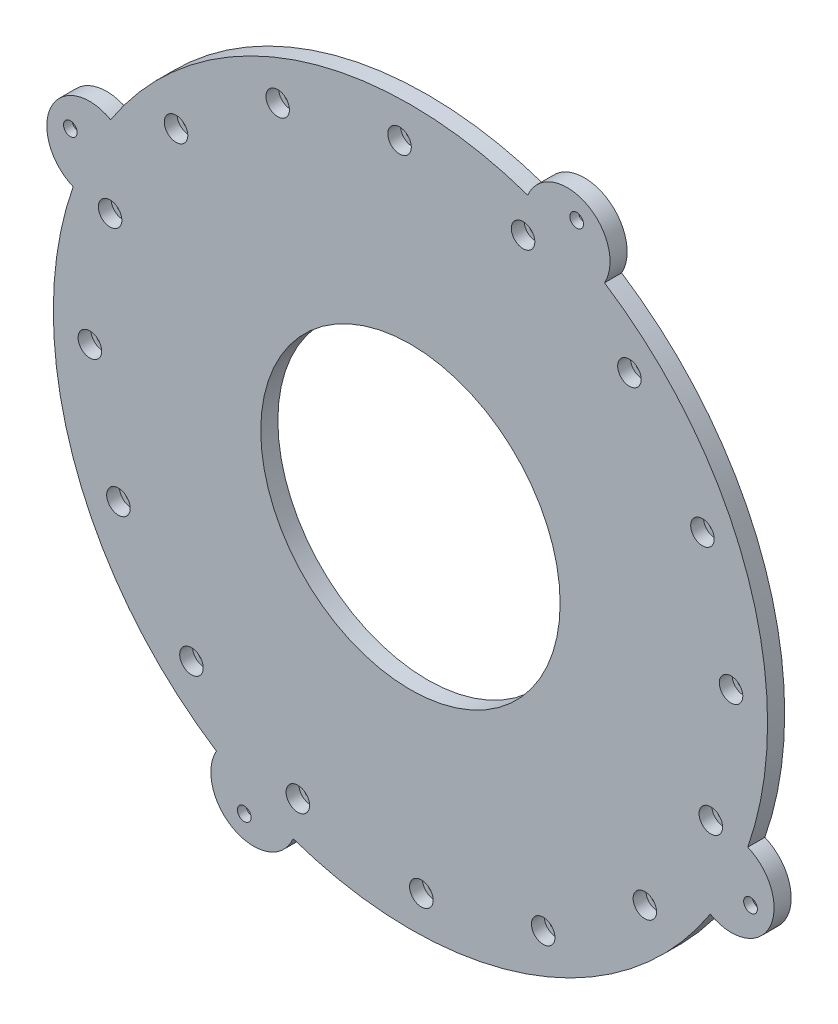
SolidWorks part; units mm, degrees
ref_plane "Front Plane" through (0, 0, 0) normal (0, 0, 1) x (1, 0, 0)
ref_plane "Top Plane" through (0, 0, 0) normal (0, 1, 0) x (1, 0, 0)
ref_plane "Right Plane" through (0, 0, 0) normal (1, 0, 0) x (0, 0, -1)
sketch "Sketch1" plane through (0, 0, 0) normal (0, 0, 1) x (1, 0, 0)
  circle A0 centre (-20.1422, -37.1244) radius 83.5
  circle A1 centre (-20.1422, -37.1244) radius 35
  circle A2 centre (-20.1422, -37.1244) radius 83.5 construction
  dimension "D1" = 70
extrude "Boss-Extrude1" add sketch "Sketch1" along normal blind 4
sketch "Sketch2" plane through (0, 0, 4) normal (0, 0, 1) x (1, 0, 0)
  circle A0 centre (-51.1825, 31.1507) radius 1.6
  circle A1 centre (-22.692, 37.8322) radius 1.6
  circle A2 centre (6.1868, 33.1023) radius 1.6
  circle A3 centre (31.0572, 17.6809) radius 1.6
  circle A4 centre (48.133, -6.084) radius 1.6
  circle A5 centre (54.8145, -34.5746) radius 1.6
  circle A6 centre (50.0845, -63.4534) radius 1.6
  circle A7 centre (34.6632, -88.3238) radius 1.6
  circle A8 centre (10.8982, -105.3996) radius 1.6
  circle A9 centre (-17.5924, -112.0811) radius 1.6
  circle A10 centre (-46.4711, -107.3511) radius 1.6
  circle A11 centre (-71.3415, -91.9297) radius 1.6
  circle A12 centre (-88.4173, -68.1648) radius 1.6
  circle A13 centre (-95.0988, -39.6742) radius 1.6
  circle A14 centre (-90.3688, -10.7954) radius 1.6
  circle A15 centre (-74.9475, 14.075) radius 1.6
  point P36 (-20.1422, -37.1244)
  dimension "D1" = 3.2
  dimension "D2" = 16
extrude "Cut-Extrude1" cut sketch "Sketch2" against normal up to next
sketch "Sketch3" plane through (0, 0, 4) normal (0, 0, 1) x (1, 0, 0)
  circle A0 centre (-74.9475, 14.075) radius 2.75
  circle A1 centre (-51.1825, 31.1507) radius 2.75
  circle A2 centre (-22.692, 37.8322) radius 2.75
  circle A3 centre (6.1868, 33.1023) radius 2.75
  circle A4 centre (31.0572, 17.6809) radius 2.75
  circle A5 centre (48.133, -6.084) radius 2.75
  circle A6 centre (54.8145, -34.5746) radius 2.75
  circle A7 centre (50.0845, -63.4534) radius 2.75
  circle A8 centre (34.6632, -88.3238) radius 2.75
  circle A9 centre (10.8982, -105.3996) radius 2.75
  circle A10 centre (-17.5924, -112.0811) radius 2.75
  circle A11 centre (-46.4711, -107.3511) radius 2.75
  circle A12 centre (-71.3415, -91.9297) radius 2.75
  circle A13 centre (-88.4173, -68.1648) radius 2.75
  circle A14 centre (-95.0988, -39.6742) radius 2.75
  circle A15 centre (-90.3688, -10.7954) radius 2.75
  point P35 (-20.1422, -37.1244)
  dimension "D1" = 5.5
  dimension "D2" = 16
extrude "Cut-Extrude2" cut sketch "Sketch3" against normal blind 3
sketch "Sketch4" plane through (0, 0, 4) normal (0, 0, 1) x (1, 0, 0)
  arc A0 (7.2931, 41.7398) -> (25.2294, 32.9732) centre (16.5242, 37.8944) cw
  circle A1 centre (-20.1422, -37.1244) radius 83.5 construction
  arc A2 (7.2931, 41.7398) -> (25.2294, 32.9732) centre (-20.1422, -37.1244) cw
  arc A3 (58.722, -64.5596) -> (49.9554, -82.496) centre (-20.1422, -37.1244) cw
  arc A4 (58.722, -64.5596) -> (49.9554, -82.496) centre (54.8767, -73.7908) cw
  arc A5 (-47.5774, -115.9886) -> (-65.5137, -107.222) centre (-20.1422, -37.1244) cw
  arc A6 (-47.5774, -115.9886) -> (-65.5137, -107.222) centre (-56.8085, -112.1433) cw
  arc A7 (-99.0063, -9.6892) -> (-90.2397, 8.2472) centre (-20.1422, -37.1244) cw
  arc A8 (-99.0063, -9.6892) -> (-90.2397, 8.2472) centre (-95.161, -0.4581) cw
  dimension "D1" = 10
  dimension "D2" = 4
extrude "Boss-Extrude2" add sketch "Sketch4" against normal up to surface (4 mm away) up to face at (-21.092, 37.8322, 0)
sketch "Sketch5" plane through (0, 0, 0) normal (0, 0, -1) x (-1, 0, 0)
  line L0 (61.1997, -121.1276) -> (56.8085, -112.1433) construction
  arc A0 (47.5774, -115.9886) -> (65.5137, -107.222) centre (56.8085, -112.1433) ccw construction
  circle A1 centre (59.0041, -116.6354) radius 1.6
  circle A2 centre (-59.3688, -75.9864) radius 1.6
  circle A3 centre (-18.7198, 42.3866) radius 1.6
  circle A4 centre (99.6532, 1.7375) radius 1.6
  point P17 (20.1422, -37.1244)
  dimension "D1" = 3.2
  dimension "D2" = 4
extrude "Cut-Extrude3" cut sketch "Sketch5" against normal up to next
sketch "Sketch6" plane through (0, 0, 0) normal (0, 0, -1) x (-1, 0, 0)
  line L0 (-56.101, -76.3756) -> (-57.3978, -73.351)
  line L1 (55.9795, -117.9322) -> (58.6148, -119.9032)
  line L2 (58.6148, -119.9032) -> (61.6395, -118.6064)
  line L3 (61.6395, -118.6064) -> (62.0287, -115.3386)
  line L4 (62.0287, -115.3386) -> (59.3934, -113.3676)
  line L5 (59.3934, -113.3676) -> (56.3687, -114.6644)
  line L6 (56.3687, -114.6644) -> (55.9795, -117.9322)
  line L7 (-58.0721, -79.011) -> (-56.101, -76.3756)
  line L8 (-61.3399, -78.6217) -> (-58.0721, -79.011)
  line L9 (-62.6366, -75.5971) -> (-61.3399, -78.6217)
  line L10 (-60.6656, -72.9617) -> (-62.6366, -75.5971)
  line L11 (-57.3978, -73.351) -> (-60.6656, -72.9617)
  line L12 (-19.1091, 39.1188) -> (-16.0844, 40.4156)
  line L13 (-21.7444, 41.0898) -> (-19.1091, 39.1188)
  line L14 (-21.3551, 44.3576) -> (-21.7444, 41.0898)
  line L15 (-18.3305, 45.6544) -> (-21.3551, 44.3576)
  line L16 (-15.6952, 43.6834) -> (-18.3305, 45.6544)
  line L17 (-16.0844, 40.4156) -> (-15.6952, 43.6834)
  line L18 (96.3854, 2.1268) -> (97.6821, -0.8978)
  line L19 (98.3564, 4.7622) -> (96.3854, 2.1268)
  line L20 (101.6242, 4.3729) -> (98.3564, 4.7622)
  line L21 (102.921, 1.3483) -> (101.6242, 4.3729)
  line L22 (100.9499, -1.2871) -> (102.921, 1.3483)
  line L23 (97.6821, -0.8978) -> (100.9499, -1.2871)
  circle A0 centre (59.0041, -116.6354) radius 2.85 construction
  point P30 (20.1422, -37.1244)
  dimension "D1" = 5.7
  dimension "D2" = 4
extrude "Cut-Extrude4" cut sketch "Sketch6" against normal blind 2
